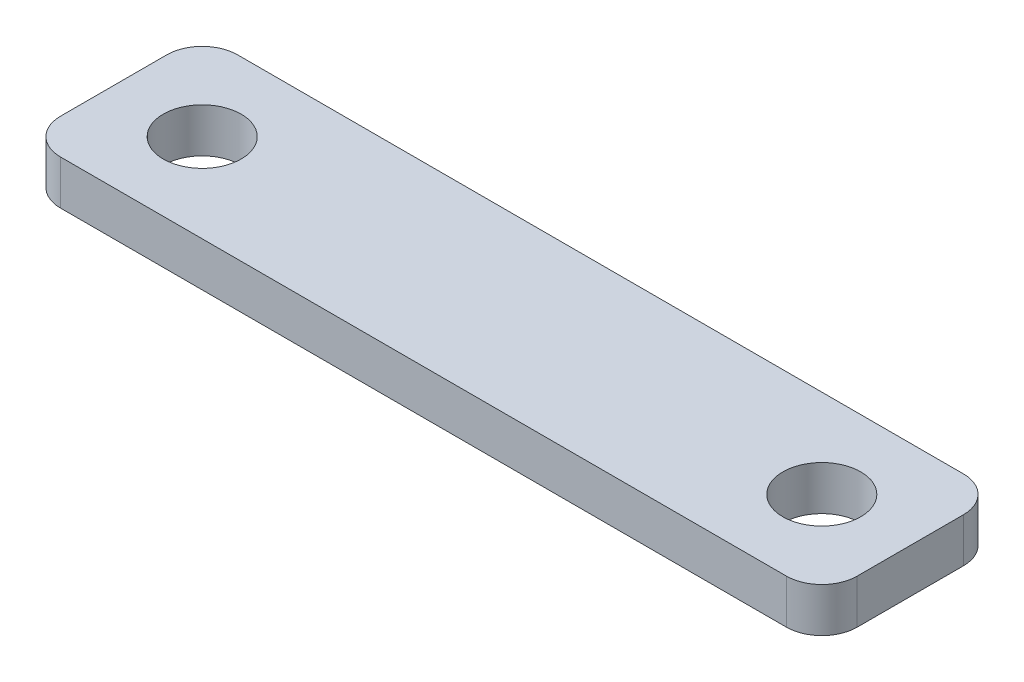
SolidWorks part; units mm, degrees
ref_plane "Front Plane" through (0, 0, 0) normal (0, 0, 1) x (1, 0, 0)
ref_plane "Top Plane" through (0, 0, 0) normal (0, 1, 0) x (1, 0, 0)
ref_plane "Right Plane" through (0, 0, 0) normal (1, 0, 0) x (0, 0, -1)
sketch "Sketch1" plane through (0, 0, 0) normal (0, 1, 0) x (1, 0, 0)
  line L0 (-55, 0) -> (55, 0) construction
  line L2 (-26.035, -6.35) -> (26.035, -6.35)
  line L3 (-28.575, -3.81) -> (-28.575, 3.81)
  line L4 (-26.035, 6.35) -> (26.035, 6.35)
  line L5 (28.575, -3.81) -> (28.575, 3.81)
  line L6 (-28.575, -6.35) -> (28.575, 6.35) construction
  line L7 (-28.575, 6.35) -> (28.575, -6.35) construction
  circle A0 centre (-22.225, 0) radius 2.794
  circle A1 centre (22.225, 0) radius 2.794
  arc A2 (26.035, 6.35) -> (28.575, 3.81) centre (26.035, 3.81) cw
  arc A3 (26.035, -6.35) -> (28.575, -3.81) centre (26.035, -3.81) ccw
  arc A4 (-26.035, -6.35) -> (-28.575, -3.81) centre (-26.035, -3.81) cw
  arc A5 (-28.575, 3.81) -> (-26.035, 6.35) centre (-26.035, 3.81) cw
  point P6 (0, 0)
  dimension "D1" = 44.45
  dimension "D2" = 5.588
  dimension "D3" = 6.35
  dimension "D4" = 6.35
  dimension "D6" = 2.54
  dimension "D5" = 12.7
extrude "Boss-Extrude1" add sketch "Sketch1" along normal blind 3.175
